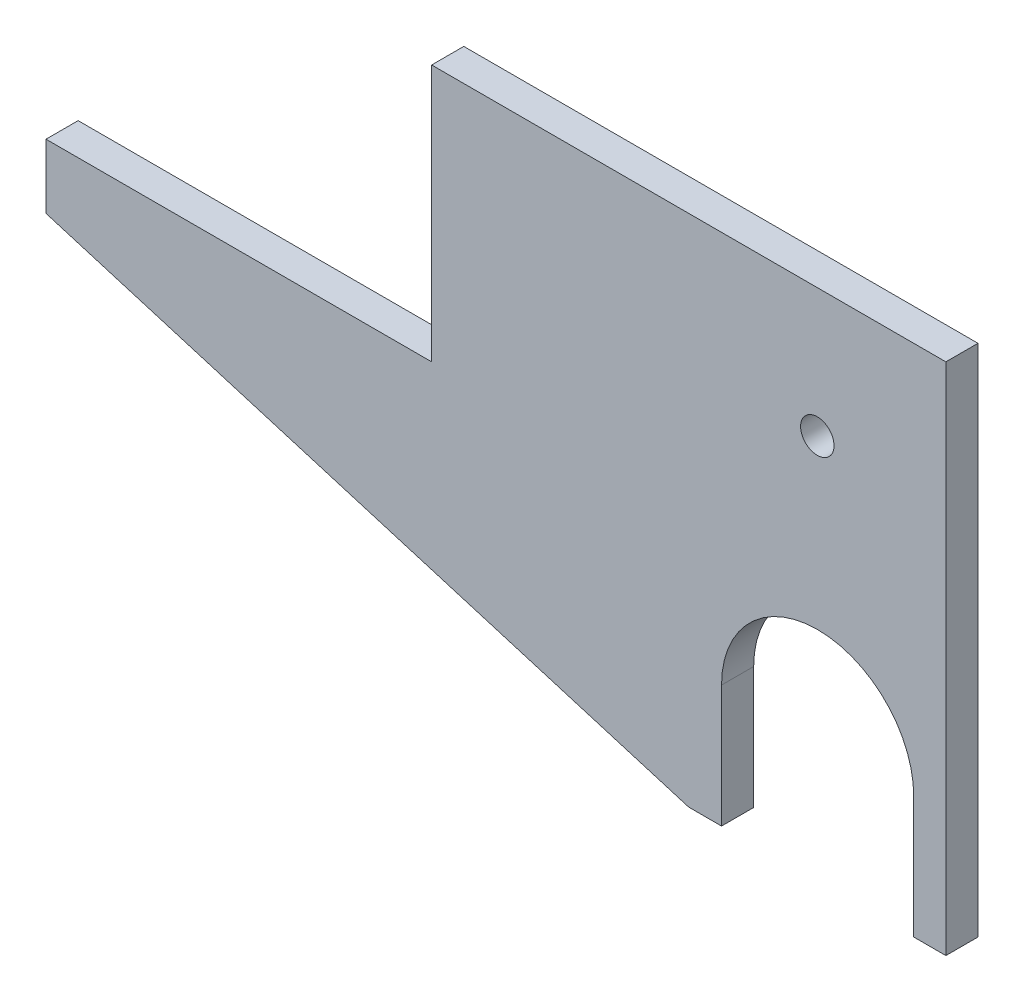
SolidWorks part; units mm, degrees
material "6061 Alloy"
ref_plane "Front Plane" through (0, 0, 0) normal (0, 0, 1) x (1, 0, 0)
ref_plane "Top Plane" through (0, 0, 0) normal (0, 1, 0) x (1, 0, 0)
ref_plane "Right Plane" through (0, 0, 0) normal (1, 0, 0) x (0, 0, -1)
sketch "Sketch1" plane through (0, 0, 0) normal (0, 0, 1) x (1, 0, 0)
  line L0 (838.2, 0) -> (838.2, -12.7)
  line L1 (838.2, 0) -> (914.4, 0)
  line L2 (838.2, -12.7) -> (965.2, -50.8)
  line L3 (914.4, 0) -> (914.4, 50.8)
  line L4 (914.4, 50.8) -> (965.2, 50.8)
  line L5 (965.2, 50.8) -> (1016, 50.8)
  line L6 (1016, -355.6) -> (1016, 381) construction
  line L7 (1016, 50.8) -> (1016, -50.8)
  line L8 (1016, -50.8) -> (1009.65, -50.8)
  line L9 (965.2, 381) -> (965.2, -355.6) construction
  line L12 (971.677, -26.67) -> (971.677, -50.8)
  line L13 (1009.65, -26.67) -> (1009.65, -50.8)
  line L14 (971.677, -50.8) -> (965.2, -50.8)
  arc A1 (1009.65, -26.67) -> (971.677, -26.67) centre (990.6635, -26.67) ccw
  dimension "D2" = 18.9865
  dimension "D1" = 101.6
  dimension "D3" = 6.35
  dimension "D4" = 24.13
  dimension "D5" = 76.2
  dimension "D6" = 50.8
  dimension "D8" = 12.7
  dimension "D9" = 50.8
extrude "Boss-Extrude1" add sketch "Sketch1" along normal blind 6.35
sketch "Sketch2" plane through (0, 0, 6.35) normal (0, 0, 1) x (1, 0, 0)
  line L9 (1009.65, -26.67) -> (1009.65, -50.8)
  line L10 (1009.65, -50.8) -> (1016, -50.8)
  line L11 (1016, -50.8) -> (1016, 50.8)
  line L12 (1016, 50.8) -> (914.4, 50.8)
  line L13 (914.4, 50.8) -> (914.4, 0)
  line L14 (914.4, 0) -> (838.2, 0)
  line L15 (914.4, 0) -> (838.2, 0)
  line L16 (965.2, -50.8) -> (971.677, -50.8)
  line L17 (971.677, -50.8) -> (971.677, -26.67)
  line L18 (1009.65, -26.67) -> (1009.65, -50.8)
  line L19 (1009.65, -50.8) -> (1016, -50.8)
  line L20 (1016, -50.8) -> (1016, 50.8)
  line L21 (1016, 50.8) -> (914.4, 50.8)
  line L22 (914.4, 50.8) -> (914.4, 0)
  line L25 (965.2, -50.8) -> (971.677, -50.8)
  line L26 (971.677, -50.8) -> (971.677, -26.67)
  line L27 (838.2, 0) -> (838.2, -12.7)
  line L30 (838.2, 0) -> (838.2, -12.7)
  line L31 (838.2, -12.7) -> (965.2, -50.8)
  line L32 (838.2, -12.7) -> (965.2, -50.8)
  arc A1 (1009.65, -26.67) -> (971.677, -26.67) centre (990.6635, -26.67) ccw
  arc A2 (1009.65, -26.67) -> (971.677, -26.67) centre (990.6635, -26.67) ccw
  circle A3 centre (990.6, 25.4) radius 3.302
  dimension "D2" = 6.604
  dimension "D3" = 25.4
  dimension "D4" = 25.4
  dimension "D1" = 0
extrude "Cut-Extrude3" cut sketch "Sketch2" against normal blind 6.35 contours A3
